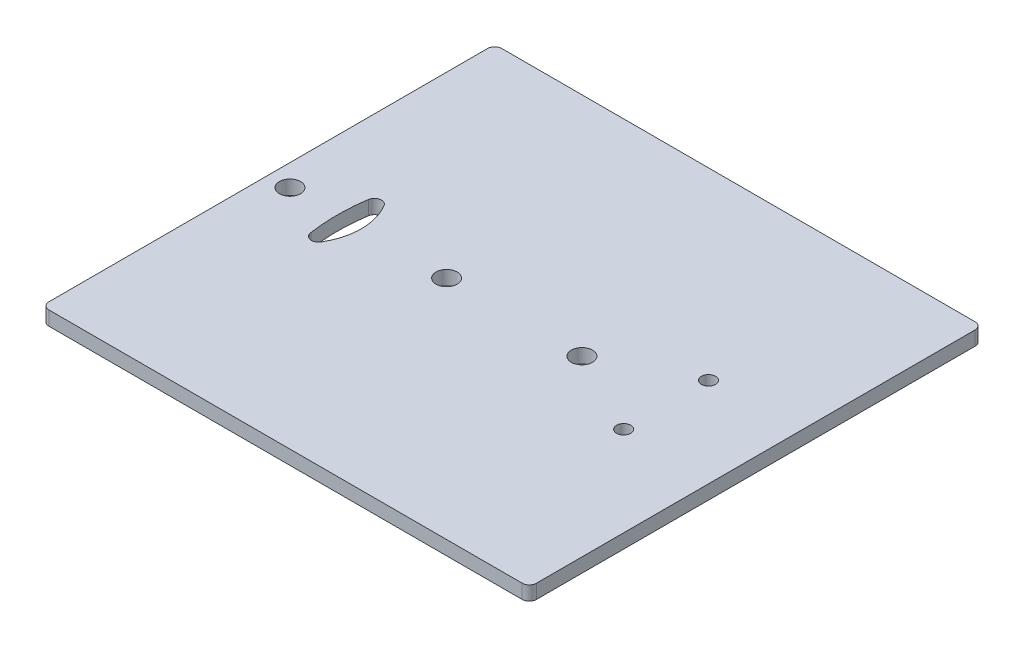
SolidWorks part; units mm, degrees
ref_plane "Alzado" through (0, 0, 0) normal (0, 0, 1) x (1, 0, 0)
ref_plane "Planta" through (0, 0, 0) normal (0, 1, 0) x (1, 0, 0)
ref_plane "Vista lateral" through (0, 0, 0) normal (1, 0, 0) x (0, 0, -1)
sketch "Croquis1" plane through (0, 0, 0) normal (0, 1, 0) x (1, 0, 0)
  line L0 (-69.5291, 32.7592) -> (-69.5291, -31.34)
  line L1 (-69.5291, -31.34) -> (-0.5291, -31.34)
  line L2 (-0.5291, -31.34) -> (-0.5291, 32.7592)
  line L3 (-0.5291, 32.7592) -> (-69.5291, 32.7592)
  circle A0 centre (-66.4576, 0.7096) radius 1.5
  arc A1 (-57.6115, 5.1805) -> (-59.4544, 4.8107) centre (-58.4657, 4.6606) ccw
  arc A2 (-59.4695, -3.2908) -> (-57.5568, -3.6702) centre (-58.4657, -3.2413) ccw
  arc A3 (-57.6672, -3.8516) -> (-57.6115, 5.1805) centre (-64.9576, 0.7096) ccw
  arc A4 (-59.4544, 4.8107) -> (-59.4389, -3.4919) centre (-32.4352, 0.7096) ccw
  circle A5 centre (-44.2866, 0.7096) radius 1.5
  circle A6 centre (-25.1301, 0.7096) radius 1.5
  circle A7 centre (-13.222, 6.7096) radius 1
  circle A8 centre (-13.222, -5.2904) radius 1
extrude "Saliente-Extruir1" add sketch "Croquis1" along normal blind 2 contours L2 L3 L0 L1 A8 A7 A6 A5 A4 A1 A3 A2 A0
fillet "Redondeo1" radius 1 4 edges at (-0.5291, 1, -32.7592) (-69.5291, 1, -32.7592) (-0.5291, 1, 31.34) (-69.5291, 1, 31.34)
